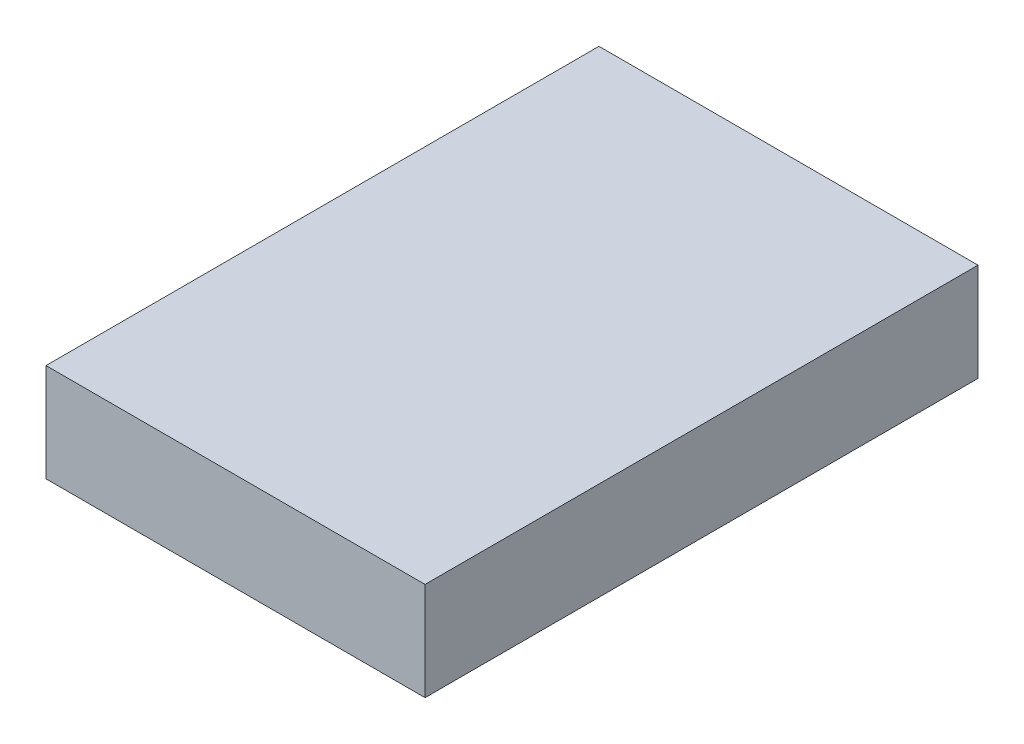
SolidWorks part; units mm, degrees
ref_plane "Спереди" through (0, 0, 0) normal (0, 0, 1) x (1, 0, 0)
ref_plane "Сверху" through (0, 0, 0) normal (0, 1, 0) x (1, 0, 0)
ref_plane "Справа" through (0, 0, 0) normal (1, 0, 0) x (0, 0, -1)
sketch "Эскиз1" plane through (0, 0, 0) normal (0, 1, 0) x (1, 0, 0)
  line L1 (-42.5, 62) -> (42.5, 62)
  line L2 (-42.5, 62) -> (-42.5, -62)
  line L3 (-42.5, -62) -> (42.5, -62)
  line L4 (42.5, 62) -> (42.5, -62)
  line L5 (-42.5, 62) -> (42.5, -62) construction
  line L6 (-42.5, -62) -> (42.5, 62) construction
  point P0 (0, 0)
extrude "Бобышка-Вытянуть1" add sketch "Эскиз1" along normal blind 22
